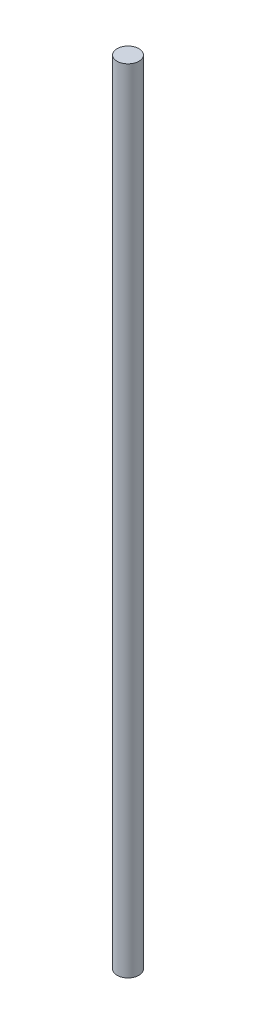
SolidWorks part; units mm, degrees
ref_plane "Front Plane" through (0, 0, 0) normal (0, 0, 1) x (1, 0, 0)
ref_plane "Top Plane" through (0, 0, 0) normal (0, 1, 0) x (1, 0, 0)
ref_plane "Right Plane" through (0, 0, 0) normal (1, 0, 0) x (0, 0, -1)
sketch "Sketch1" plane through (0, 0, 0) normal (0, 1, 0) x (1, 0, 0)
  circle A0 centre (0, 0) radius 1.7526
  dimension "D1" = 3.5052
extrude "Boss-Extrude1" add sketch "Sketch1" along normal blind 127
